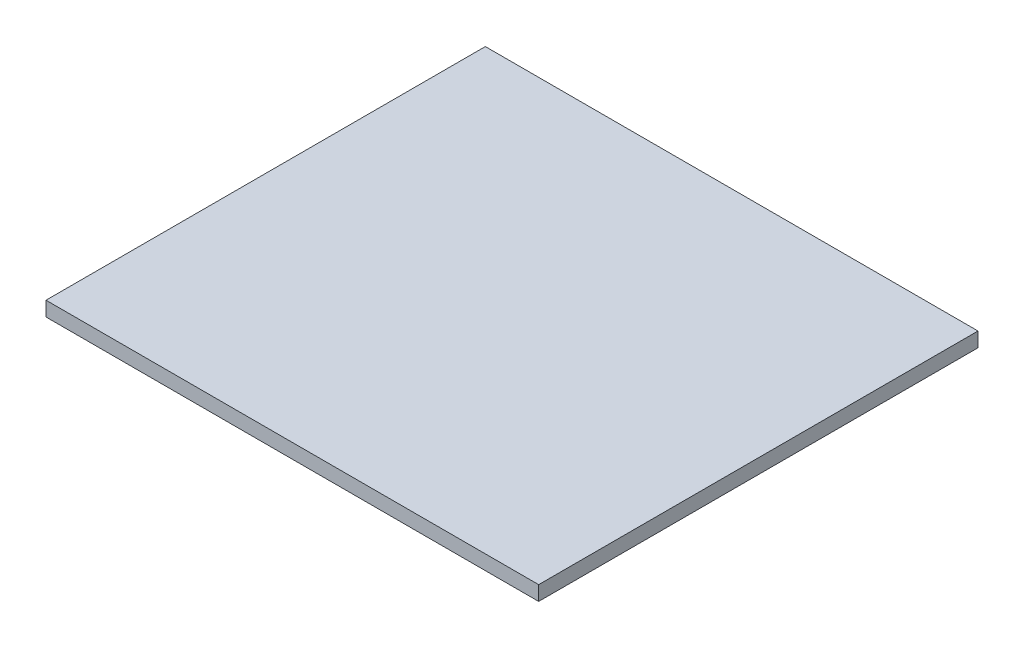
SolidWorks part; units mm, degrees
ref_plane "Alzado" through (0, 0, 0) normal (0, 0, 1) x (1, 0, 0)
ref_plane "Planta" through (0, 0, 0) normal (0, 1, 0) x (1, 0, 0)
ref_plane "Vista lateral" through (0, 0, 0) normal (1, 0, 0) x (0, 0, -1)
sketch "Croquis1" plane through (0, 0, 0) normal (0, 1, 0) x (1, 0, 0)
  line L1 (-461.9, -411.9) -> (461.9, -411.9)
  line L2 (-461.9, -411.9) -> (-461.9, 411.9)
  line L3 (-461.9, 411.9) -> (461.9, 411.9)
  line L4 (461.9, -411.9) -> (461.9, 411.9)
  line L5 (-461.9, -411.9) -> (461.9, 411.9) construction
  line L6 (-461.9, 411.9) -> (461.9, -411.9) construction
  point P0 (0, 0)
  dimension "D1" = 923.8
  dimension "D2" = 823.8
extrude "Saliente-Extruir1" add sketch "Croquis1" along normal blind 1.9
sketch "Croquis2" plane through (0, 0, 0) normal (0, -1, 0) x (1, 0, 0)
  line L0 (-460, 410) -> (-460, -410)
  line L1 (-461.9, 411.9) -> (461.9, 411.9)
  line L2 (-461.9, 411.9) -> (-461.9, -411.9)
  line L3 (-461.9, -411.9) -> (461.9, -411.9)
  line L4 (461.9, 411.9) -> (461.9, -411.9)
  line L5 (-460, -410) -> (460, -410)
  line L6 (460, 410) -> (460, -410)
  line L7 (-460, 410) -> (460, 410)
  dimension "D1" = 1.9
extrude "Saliente-Extruir2" add sketch "Croquis2" along normal blind 25.4
